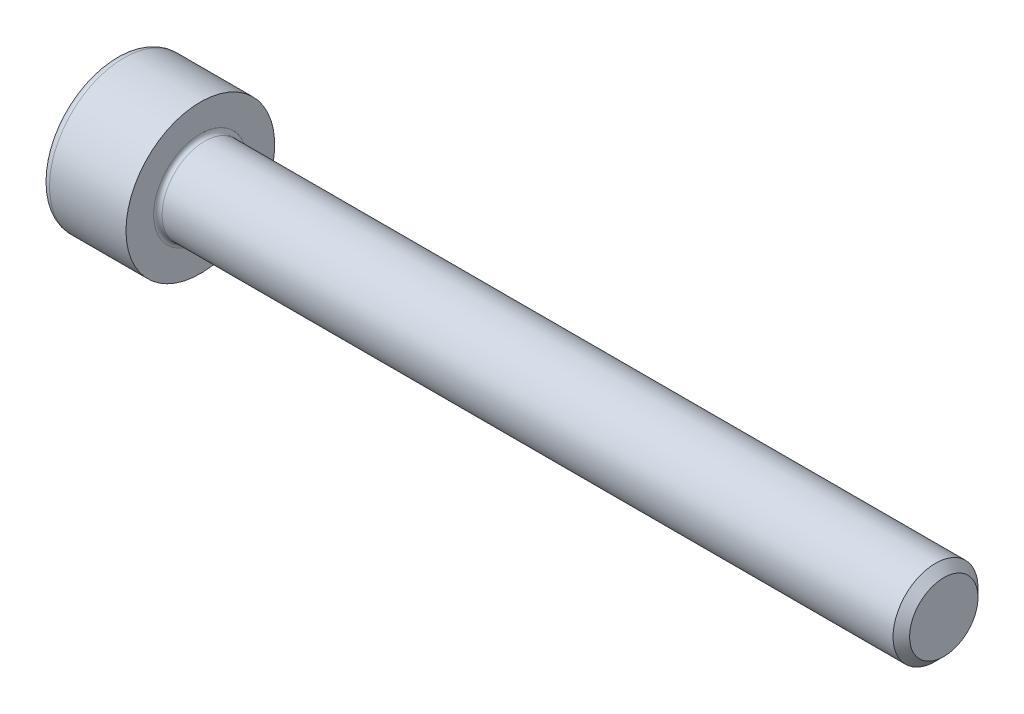
SolidWorks part; units mm, degrees
revolve "Base-Revolve" add sketch "BodySke"
sketch "BodySke" plane through (0, 0, 0) normal (0, 0, 1) x (1, 0, 0)
  line L0 (0, 0) -> (0, 3.5)
  line L1 (0, 3.5) -> (4, 3.5)
  line L2 (4, 3.5) -> (4, 2)
  line L3 (4, 2) -> (38.61, 2)
  line L4 (39, 1.61) -> (39, 0)
  line L5 (39, 0) -> (0, 0)
  line L6 (-31.75, 0) -> (127, 0) construction
  line L8 (39, 1.61) -> (38.61, 2)
  line L10 (39, -1.61) -> (38.61, -2) construction
  line L11 (4.7, 9.525) -> (4.7, 3.175) construction
  line L12 (19, 9.525) -> (19, 3.175) construction
  line L13 (-21, 9.525) -> (-21, 3.175) construction
  dimension "Head_ht" = 4
  dimension "Length" = 35
  dimension "Body_ch_ang" = 45
  dimension "Diameter" = 4
  dimension "Minor_dia" = 3.22
  dimension "Advance" = 0.7
  dimension "Thread_nom" = 20
  dimension "Thread_length" = 60
  dimension "Head_dia" = 7
cosmetic thread "ThreadCosmetic" [suppressed]
fillet "Fillet1" radius 0.2 1 edges at (4, 0, 2)
fillet "Fillet2" radius 0.4 1 edges at (0, 0, 3.5)
ref_plane "Plane1" through (0, 0, 0) normal (0, 0, 1) x (1, 0, 0)
ref_plane "Plane2" through (0, 0, 0) normal (0, 1, 0) x (1, 0, 0)
ref_plane "Plane3" through (0, 0, 0) normal (1, 0, 0) x (0, 0, -1)
sketch "Sketch2" plane through (0, 0, 0) normal (0, 0, 1) x (1, 0, 0)
  line L0 (0, 1.51) -> (2, 1.51)
  line L1 (2, 1.51) -> (2.8718, 0)
  line L2 (-31.75, 0) -> (127, 0) construction
  line L3 (2.8718, 0) -> (0, 0)
  line L4 (0, 0) -> (0, 1.51)
  line L6 (0, 0) -> (47.625, 0) construction
  dimension "D1" = 1.51
  dimension "D2" = 60
  dimension "Depth" = 2
revolve "Hex-PreBroach" cut sketch "Sketch2" angle 360 about L6
sketch "Sketch3" plane through (0, 0, 0) normal (-1, 0, 0) x (0, 0.5, 0.866)
  line L0 (0.8718, 1.51) -> (-0.8718, 1.51)
  line L1 (-0.8718, 1.51) -> (-1.7436, 0)
  line L2 (0.8718, 1.51) -> (1.7436, 0)
  line L3 (0.8718, -1.51) -> (1.7436, 0)
  line L4 (0.8718, -1.51) -> (-0.8718, -1.51)
  line L5 (-0.8718, -1.51) -> (-1.7436, 0)
  dimension "D1" = 1.51
  dimension "D2" = 1.51
  dimension "Hex_size" = 3.02
extrude "Hex" cut sketch "Sketch3" against normal blind 2
sketch "ThdSchSke" plane through (0, 0, 0) normal (0, 0, 1) x (1, 0, 0)
  line L0 (19, -1.61) -> (18.7269, -2)
  line L1 (19, -1.61) -> (19.2731, -2)
  line L2 (19.2731, -2) -> (19.2731, -2.5)
  line L3 (-3.175, 0) -> (5.1513, 0) construction
  line L4 (0, 3.1) -> (0, -3.1) construction
  line L5 (19.2731, -2.5) -> (18.7269, -2.5)
  line L6 (18.7269, -2.5) -> (18.7269, -2)
  dimension "Thread_minor" = 3.22
  dimension "Diameter" = 4
  dimension "Start" = 19
revolve "ThreadSchematic" [suppressed] cut sketch "ThdSchSke" angle 360 about L3
pattern_linear "ThdSchPat" [suppressed]
equation "\"D2@Sketch3\" = \"Hex_size@Sketch3\" / 2"
equation "\"D1@Sketch3\" = \"Hex_size@Sketch3\" / 2"
equation "\"D1@Sketch2\" = \"Hex_size@Sketch3\" / 2"
equation "\"Thread_minor@ThreadCosmetic\"  =  \"Minor_dia@BodySke\""
equation "\"Depth@Sketch2\" =  \"Key_eng@Hex\""
equation "\"Thread_length@ThreadCosmetic\" = ((sgn( (\"Length@BodySke\" - \"Advance@BodySke\" * 3.0) - \"Thread_nom@BodySke\" )-1)*( (\"Length@BodySke\" - \"Advance@BodySke\" * 3.0) - \"Thread_nom@BodySke\" ))/-2+ \"Thread_nom@BodySke\""
equation "\"Thread_minor@ThdSchSke\" = \"Minor_dia@BodySke\""
equation "\"Diameter@ThdSchSke\" = \"Diameter@BodySke\""
equation "\"Overcut@ThdSchSke\" = \"Diameter@BodySke\" * 1.25"
equation "\"Start@ThdSchSke\" = \"Head_ht@BodySke\" + \"Length@BodySke\" - \"Thread_length@ThreadCosmetic\"  '---Non-countersunk---"
equation "\"Num_threads@ThdSchPat\" = int( \"Thread_length@ThreadCosmetic\" / \"Advance@BodySke\" + 0.999 )  + 1"
equation "\"Advance@ThdSchPat\" = \"Thread_length@ThreadCosmetic\" /  (\"Num_threads@ThdSchPat\" - 1) 'relax it"
equation "\"Num_threads@ThdSchPat\" = \"Num_threads@ThdSchPat\" - sgn( \"Num_threads@ThdSchPat\" - 1) '---chamfered tips only---"
